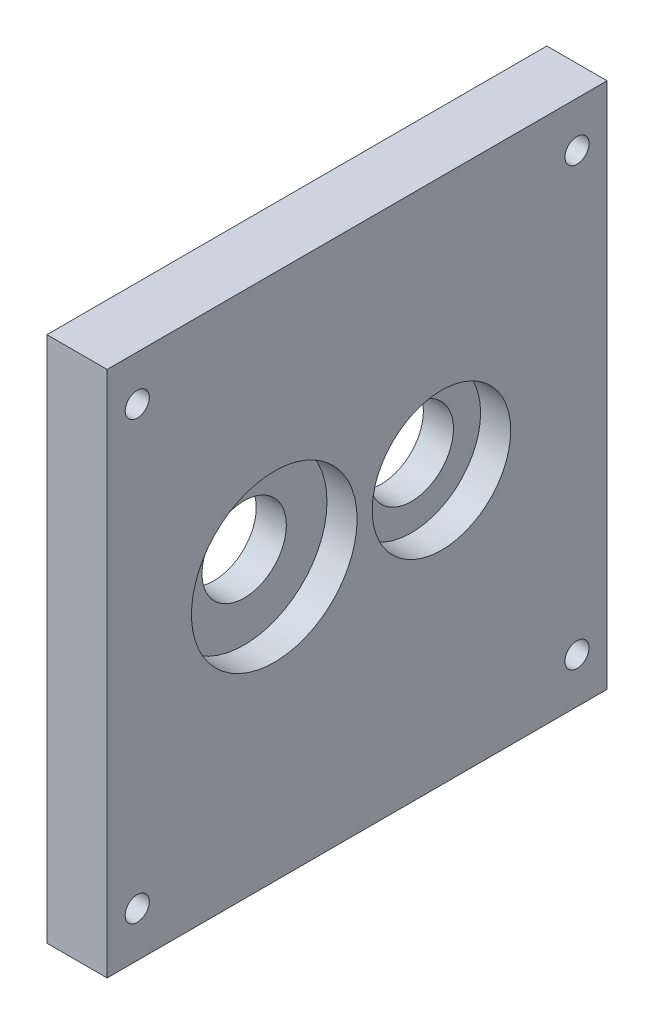
SolidWorks part; units mm, degrees
material "201 Annealed Stainless Steel (SS)"
ref_plane "Front Plane" through (0, 0, 0) normal (0, 0, 1) x (1, 0, 0)
ref_plane "Top Plane" through (0, 0, 0) normal (0, 1, 0) x (1, 0, 0)
ref_plane "Right Plane" through (0, 0, 0) normal (1, 0, 0) x (0, 0, -1)
sketch "Sketch1" plane through (0, 0, 0) normal (0, 1, 0) x (1, 0, 0)
  line L0 (-55, 0) -> (55, 0) construction
  line L1 (10, 83) -> (-10, 83)
  line L2 (10, 83) -> (10, -83)
  line L3 (10, -83) -> (-10, -83)
  line L4 (-10, 83) -> (-10, -83)
  line L5 (0, -55) -> (0, 55) construction
  point P6 (-10, 0)
  point P7 (0, -83)
  dimension "D1" = 166
  dimension "D2" = 20
extrude "Boss-Extrude1" add sketch "Sketch1" along normal blind 175
sketch "Sketch2" plane through (10, 0, 0) normal (1, 0, 0) x (0, 0, -1)
  circle A0 centre (-27.5, 90.5) radius 14 construction
  circle A1 centre (28, 90.5) radius 14 construction
  circle A2 centre (-27.5, 90.5) radius 14
  circle A3 centre (28, 90.5) radius 14
extrude "Cut-Extrude1" cut sketch "Sketch2" against normal blind 175
sketch "Sketch3" plane through (10, 0, 0) normal (1, 0, 0) x (0, 0, -1)
  circle A0 centre (-27.5, 90.5) radius 27.5 construction
  circle A1 centre (28, 90.5) radius 23 construction
  circle A2 centre (-27.5, 90.5) radius 27.5
  circle A3 centre (28, 90.5) radius 23
extrude "Cut-Extrude2" cut sketch "Sketch3" against normal blind 10
sketch "Sketch4" plane through (10, 0, 0) normal (1, 0, 0) x (0, 0, -1)
  line L0 (-83, 175) -> (83, 175) construction
  line L1 (83, 175) -> (83, 0) construction
  line L2 (83, 87.5) -> (-83, 87.5) construction
  line L3 (0, 87.5) -> (0, 175) construction
  circle A0 centre (73, 160) radius 4
  circle A1 centre (73, 15) radius 4
  circle A2 centre (-73, 15) radius 4
  circle A3 centre (-73, 160) radius 4
  dimension "D1" = 8
  dimension "D2" = 15
  dimension "D3" = 10
extrude "Cut-Extrude3" cut sketch "Sketch4" against normal through all
